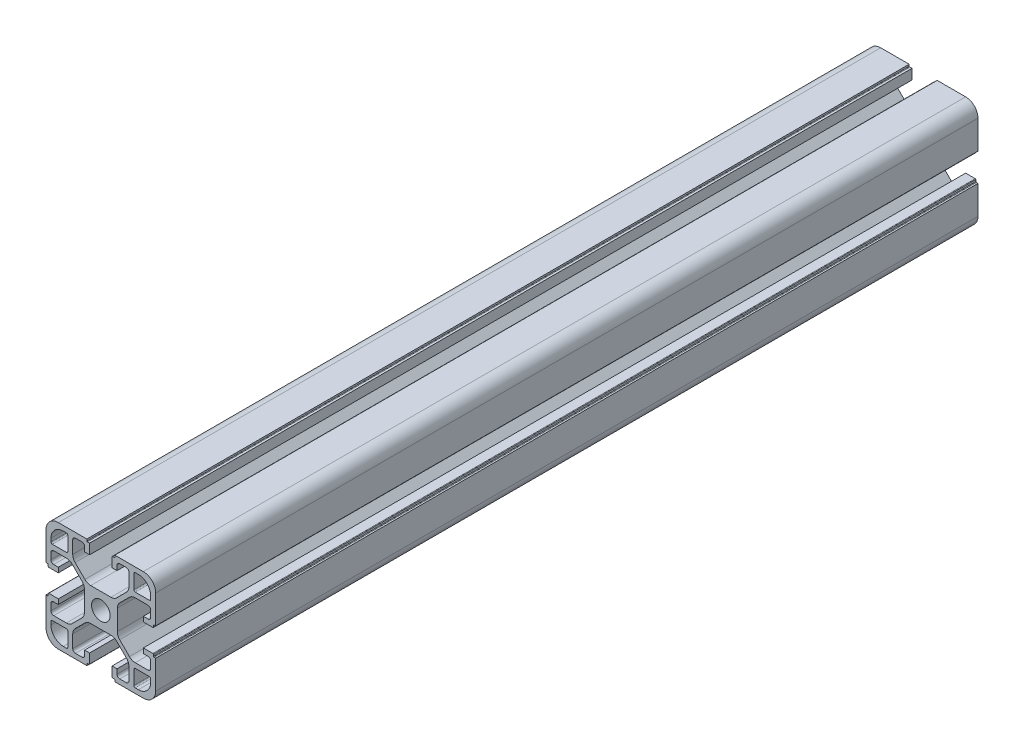
SolidWorks part; units mm, degrees
ref_plane "Front Plane" through (0, 0, 0) normal (0, 0, 1) x (1, 0, 0)
ref_plane "Top Plane" through (0, 0, 0) normal (0, 1, 0) x (1, 0, 0)
ref_plane "Right Plane" through (0, 0, 0) normal (1, 0, 0) x (0, 0, -1)
sketch "Sketch1" plane through (0, 0, 0) normal (0, 0, 1) x (1, 0, 0)
  line L0 (84.1702, 31.7204) -> (84.1702, 42.1204)
  line L1 (44.1702, 62.7204) -> (44.1702, 52.3204)
  line L2 (48.6702, 27.2204) -> (59.0702, 27.2204)
  line L3 (79.6702, 67.2204) -> (69.2702, 67.2204)
  line L4 (84.1702, 52.3204) -> (84.1702, 62.7204)
  line L5 (58.8702, 67.2204) -> (48.6702, 67.2204)
  line L6 (44.1702, 42.1204) -> (44.1702, 31.7204)
  line L7 (69.2702, 27.2204) -> (79.6702, 27.2204)
  line L8 (48.6702, 27.2204) -> (59.0702, 27.2204)
  line L9 (44.1702, 42.1204) -> (44.1702, 31.7204)
  line L10 (44.1702, 42.1204) -> (44.7702, 42.1204)
  line L11 (44.9702, 42.3204) -> (44.9702, 42.9204)
  line L12 (48.6702, 43.1204) -> (45.1702, 43.1204)
  line L13 (48.6702, 41.3204) -> (48.6702, 43.1204)
  line L14 (46.9702, 41.3204) -> (48.6702, 41.3204)
  line L15 (45.9702, 37.9704) -> (45.9702, 40.3204)
  line L16 (51.6169, 36.9704) -> (46.9702, 36.9704)
  line L17 (57.2915, 41.4024) -> (53.7382, 37.8491)
  line L18 (58.1702, 50.9171) -> (58.1702, 43.5237)
  line L19 (53.7382, 56.5917) -> (57.2915, 53.0384)
  line L20 (46.9702, 57.4704) -> (51.6169, 57.4704)
  line L21 (45.9702, 54.1204) -> (45.9702, 56.4704)
  line L22 (48.6702, 53.1204) -> (46.9702, 53.1204)
  line L23 (48.6702, 51.3204) -> (48.6702, 53.1204)
  line L24 (45.1702, 51.3204) -> (48.6702, 51.3204)
  line L25 (44.9702, 51.5204) -> (44.9702, 52.1204)
  line L26 (44.7702, 52.3204) -> (44.1702, 52.3204)
  line L27 (44.1702, 62.7204) -> (44.1702, 52.3204)
  line L28 (59.0702, 67.2204) -> (48.6702, 67.2204)
  line L29 (59.0702, 67.2204) -> (59.0702, 66.6204)
  line L30 (59.2702, 66.4204) -> (60.0702, 66.4204)
  line L31 (60.0702, 62.7204) -> (60.0702, 66.4204)
  line L32 (58.2702, 62.7204) -> (60.0702, 62.7204)
  line L33 (58.2702, 64.4204) -> (58.2702, 62.7204)
  line L34 (54.9202, 65.4204) -> (57.2702, 65.4204)
  line L35 (53.9202, 59.7737) -> (53.9202, 64.4204)
  line L36 (58.3522, 54.0991) -> (54.7989, 57.6524)
  line L37 (67.8669, 53.2204) -> (60.4735, 53.2204)
  line L38 (73.5415, 57.6524) -> (69.9882, 54.0991)
  line L39 (74.4202, 64.4204) -> (74.4202, 59.7737)
  line L40 (71.0702, 65.4204) -> (73.4202, 65.4204)
  line L41 (70.0702, 62.7204) -> (70.0702, 64.4204)
  line L42 (68.2702, 62.7204) -> (70.0702, 62.7204)
  line L43 (68.2702, 66.2204) -> (68.2702, 62.7204)
  line L44 (68.4702, 66.4204) -> (69.2702, 66.4204)
  line L45 (69.2702, 66.4204) -> (69.2702, 67.2204)
  line L46 (79.6702, 67.2204) -> (69.4702, 67.2204)
  line L47 (84.1702, 52.3204) -> (84.1702, 62.7204)
  line L48 (84.1702, 52.3204) -> (83.5702, 52.3204)
  line L49 (83.3702, 52.1204) -> (83.3702, 51.5204)
  line L50 (79.6702, 51.3204) -> (83.1702, 51.3204)
  line L51 (79.6702, 53.1204) -> (79.6702, 51.3204)
  line L52 (81.3702, 53.1204) -> (79.6702, 53.1204)
  line L53 (82.3702, 56.4704) -> (82.3702, 54.1204)
  line L54 (76.7235, 57.4704) -> (81.3702, 57.4704)
  line L55 (71.0489, 53.0384) -> (74.6022, 56.5917)
  line L56 (70.1702, 43.5237) -> (70.1702, 50.9171)
  line L57 (74.6022, 37.8491) -> (71.0489, 41.4024)
  line L58 (81.3702, 36.9704) -> (76.7235, 36.9704)
  line L59 (82.3702, 40.3204) -> (82.3702, 37.9704)
  line L60 (79.6702, 41.3204) -> (81.3702, 41.3204)
  line L61 (79.6702, 43.1204) -> (79.6702, 41.3204)
  line L62 (83.1702, 43.1204) -> (79.6702, 43.1204)
  line L63 (83.3702, 42.9204) -> (83.3702, 42.3204)
  line L64 (83.5702, 42.1204) -> (84.1702, 42.1204)
  line L65 (84.1702, 31.7204) -> (84.1702, 42.1204)
  line L66 (69.2702, 27.2204) -> (79.6702, 27.2204)
  line L67 (69.2702, 27.2204) -> (69.2702, 27.8204)
  line L68 (69.0702, 28.0204) -> (68.4702, 28.0204)
  line L69 (68.2702, 31.7204) -> (68.2702, 28.2204)
  line L70 (70.0702, 31.7204) -> (68.2702, 31.7204)
  line L71 (70.0702, 30.0204) -> (70.0702, 31.7204)
  line L72 (73.4202, 29.0204) -> (71.0702, 29.0204)
  line L73 (74.4202, 34.6671) -> (74.4202, 30.0204)
  line L74 (69.9882, 40.3417) -> (73.5415, 36.7884)
  line L75 (60.4735, 41.2204) -> (67.8669, 41.2204)
  line L76 (54.7989, 36.7884) -> (58.3522, 40.3417)
  line L77 (53.9202, 30.0204) -> (53.9202, 34.6671)
  line L78 (57.2702, 29.0204) -> (54.9202, 29.0204)
  line L79 (58.2702, 31.7204) -> (58.2702, 30.0204)
  line L80 (60.0702, 31.7204) -> (58.2702, 31.7204)
  line L81 (60.0702, 28.2204) -> (60.0702, 31.7204)
  line L82 (59.8702, 28.0204) -> (59.2702, 28.0204)
  line L83 (59.0702, 27.8204) -> (59.0702, 27.2204)
  line L84 (82.3702, 34.6704) -> (82.3702, 33.5204)
  line L85 (76.7202, 35.1704) -> (81.8702, 35.1704)
  line L86 (76.2202, 29.5204) -> (76.2202, 34.6704)
  line L87 (77.8702, 29.0204) -> (76.7202, 29.0204)
  line L88 (51.6202, 29.0204) -> (50.4702, 29.0204)
  line L89 (52.1202, 34.6704) -> (52.1202, 29.5204)
  line L90 (46.4702, 35.1704) -> (51.6202, 35.1704)
  line L91 (45.9702, 33.5204) -> (45.9702, 34.6704)
  line L92 (45.9702, 59.7704) -> (45.9702, 60.9204)
  line L93 (51.6202, 59.2704) -> (46.4702, 59.2704)
  line L94 (52.1202, 64.9204) -> (52.1202, 59.7704)
  line L95 (50.4702, 65.4204) -> (51.6202, 65.4204)
  line L96 (76.7202, 65.4204) -> (77.8702, 65.4204)
  line L97 (76.2202, 59.7704) -> (76.2202, 64.9204)
  line L98 (81.8702, 59.2704) -> (76.7202, 59.2704)
  line L99 (82.3702, 60.9204) -> (82.3702, 59.7704)
  line L100 (71.0702, 65.4204) -> (73.4202, 65.4204)
  line L101 (70.0702, 62.7204) -> (70.0702, 64.4204)
  line L102 (68.2702, 62.7204) -> (70.0702, 62.7204)
  line L103 (68.2702, 66.2204) -> (68.2702, 62.7204)
  line L104 (60.0702, 62.7204) -> (60.0702, 66.2204)
  line L105 (58.2702, 62.7204) -> (60.0702, 62.7204)
  line L106 (58.2702, 64.4204) -> (58.2702, 62.7204)
  line L107 (54.9202, 65.4204) -> (57.2702, 65.4204)
  line L108 (53.9202, 59.7737) -> (53.9202, 64.4204)
  line L109 (58.3522, 54.0991) -> (54.7989, 57.6524)
  line L110 (67.8669, 53.2204) -> (60.4735, 53.2204)
  line L111 (73.5415, 57.6524) -> (69.9882, 54.0991)
  line L112 (74.4202, 64.4204) -> (74.4202, 59.7737)
  line L113 (59.2702, 66.4204) -> (59.8702, 66.4204)
  line L114 (59.0702, 67.0204) -> (59.0702, 66.6204)
  line L115 (69.2702, 66.6204) -> (69.2702, 67.0204)
  line L116 (68.4702, 66.4204) -> (69.0702, 66.4204)
  line L117 (82.3702, 40.3204) -> (82.3702, 37.9704)
  line L118 (79.6702, 41.3204) -> (81.3702, 41.3204)
  line L119 (79.6702, 43.1204) -> (79.6702, 41.3204)
  line L120 (83.1702, 43.1204) -> (79.6702, 43.1204)
  line L121 (79.6702, 51.3204) -> (83.1702, 51.3204)
  line L122 (79.6702, 53.1204) -> (79.6702, 51.3204)
  line L123 (81.3702, 53.1204) -> (79.6702, 53.1204)
  line L124 (82.3702, 56.4704) -> (82.3702, 54.1204)
  line L125 (76.7235, 57.4704) -> (81.3702, 57.4704)
  line L126 (71.0489, 53.0384) -> (74.6022, 56.5917)
  line L127 (70.1702, 43.5237) -> (70.1702, 50.9171)
  line L128 (74.6022, 37.8491) -> (71.0489, 41.4024)
  line L129 (81.3702, 36.9704) -> (76.7235, 36.9704)
  line L130 (45.9702, 54.1204) -> (45.9702, 56.4704)
  line L131 (48.6702, 53.1204) -> (46.9702, 53.1204)
  line L132 (48.6702, 51.3204) -> (48.6702, 53.1204)
  line L133 (45.1702, 51.3204) -> (48.6702, 51.3204)
  line L134 (48.6702, 43.1204) -> (45.1702, 43.1204)
  line L135 (48.6702, 41.3204) -> (48.6702, 43.1204)
  line L136 (46.9702, 41.3204) -> (48.6702, 41.3204)
  line L137 (45.9702, 37.9704) -> (45.9702, 40.3204)
  line L138 (51.6169, 36.9704) -> (46.9702, 36.9704)
  line L139 (57.2915, 41.4024) -> (53.7382, 37.8491)
  line L140 (58.1702, 50.9171) -> (58.1702, 43.5237)
  line L141 (53.7382, 56.5917) -> (57.2915, 53.0384)
  line L142 (46.9702, 57.4704) -> (51.6169, 57.4704)
  line L143 (57.2702, 29.0204) -> (54.9202, 29.0204)
  line L144 (58.2702, 31.7204) -> (58.2702, 30.0204)
  line L145 (60.0702, 31.7204) -> (58.2702, 31.7204)
  line L146 (60.0702, 28.2204) -> (60.0702, 31.7204)
  line L147 (68.2702, 31.7204) -> (68.2702, 28.2204)
  line L148 (70.0702, 31.7204) -> (68.2702, 31.7204)
  line L149 (70.0702, 30.0204) -> (70.0702, 31.7204)
  line L150 (73.4202, 29.0204) -> (71.0702, 29.0204)
  line L151 (74.4202, 34.6671) -> (74.4202, 30.0204)
  line L152 (69.9882, 40.3417) -> (73.5415, 36.7884)
  line L153 (60.4735, 41.2204) -> (67.8669, 41.2204)
  line L154 (54.7989, 36.7884) -> (58.3522, 40.3417)
  line L155 (53.9202, 30.0204) -> (53.9202, 34.6671)
  line L156 (69.0702, 28.0204) -> (68.4702, 28.0204)
  line L157 (69.2702, 27.2204) -> (69.2702, 27.8204)
  line L158 (59.0702, 27.8204) -> (59.0702, 27.2204)
  line L159 (59.8702, 28.0204) -> (59.2702, 28.0204)
  line L160 (44.9702, 42.3204) -> (44.9702, 42.9204)
  line L161 (44.1702, 42.1204) -> (44.7702, 42.1204)
  line L162 (44.7702, 52.3204) -> (44.1702, 52.3204)
  line L163 (44.9702, 51.5204) -> (44.9702, 52.1204)
  line L164 (83.3702, 52.1204) -> (83.3702, 51.5204)
  line L165 (84.1702, 52.3204) -> (83.5702, 52.3204)
  line L166 (83.5702, 42.1204) -> (84.1702, 42.1204)
  line L167 (83.3702, 42.9204) -> (83.3702, 42.3204)
  line L168 (76.2202, 59.7704) -> (76.2202, 64.9204)
  line L169 (81.8702, 59.2704) -> (76.7202, 59.2704)
  line L170 (82.3702, 60.9204) -> (82.3702, 59.7704)
  line L171 (76.7202, 65.4204) -> (77.8702, 65.4204)
  line L172 (51.6202, 59.2704) -> (46.4702, 59.2704)
  line L173 (52.1202, 64.9204) -> (52.1202, 59.7704)
  line L174 (50.4702, 65.4204) -> (51.6202, 65.4204)
  line L175 (45.9702, 59.7704) -> (45.9702, 60.9204)
  line L176 (52.1202, 34.6704) -> (52.1202, 29.5204)
  line L177 (46.4702, 35.1704) -> (51.6202, 35.1704)
  line L178 (45.9702, 33.5204) -> (45.9702, 34.6704)
  line L179 (51.6202, 29.0204) -> (50.4702, 29.0204)
  line L180 (76.7202, 35.1704) -> (81.8702, 35.1704)
  line L181 (76.2202, 29.5204) -> (76.2202, 34.6704)
  line L182 (77.8702, 29.0204) -> (76.7202, 29.0204)
  line L183 (82.3702, 34.6704) -> (82.3702, 33.5204)
  arc A0 (60.7702, 47.2204) -> (67.5702, 47.2204) centre (64.1702, 47.2204) ccw
  arc A1 (44.1702, 31.7204) -> (48.6702, 27.2204) centre (48.6702, 31.7204) ccw
  arc A2 (44.7702, 42.1204) -> (44.9702, 42.3204) centre (44.7702, 42.3204) ccw
  arc A3 (45.1702, 43.1204) -> (44.9702, 42.9204) centre (45.1702, 42.9204) ccw
  arc A4 (46.9702, 41.3204) -> (45.9702, 40.3204) centre (46.9702, 40.3204) ccw
  arc A5 (45.9702, 37.9704) -> (46.9702, 36.9704) centre (46.9702, 37.9704) ccw
  arc A6 (51.6169, 36.9704) -> (53.7382, 37.8491) centre (51.6169, 39.9704) ccw
  arc A7 (57.2915, 41.4024) -> (58.1702, 43.5237) centre (55.1702, 43.5237) ccw
  arc A8 (58.1702, 50.9171) -> (57.2915, 53.0384) centre (55.1702, 50.9171) ccw
  arc A9 (53.7382, 56.5917) -> (51.6169, 57.4704) centre (51.6169, 54.4704) ccw
  arc A10 (46.9702, 57.4704) -> (45.9702, 56.4704) centre (46.9702, 56.4704) ccw
  arc A11 (45.9702, 54.1204) -> (46.9702, 53.1204) centre (46.9702, 54.1204) ccw
  arc A12 (44.9702, 51.5204) -> (45.1702, 51.3204) centre (45.1702, 51.5204) ccw
  arc A13 (44.9702, 52.1204) -> (44.7702, 52.3204) centre (44.7702, 52.1204) ccw
  arc A14 (48.6702, 67.2204) -> (44.1702, 62.7204) centre (48.6702, 62.7204) ccw
  arc A15 (59.0702, 66.6204) -> (59.2702, 66.4204) centre (59.2702, 66.6204) ccw
  arc A16 (58.2702, 64.4204) -> (57.2702, 65.4204) centre (57.2702, 64.4204) ccw
  arc A17 (54.9202, 65.4204) -> (53.9202, 64.4204) centre (54.9202, 64.4204) ccw
  arc A18 (53.9202, 59.7737) -> (54.7989, 57.6524) centre (56.9202, 59.7737) ccw
  arc A19 (58.3522, 54.0991) -> (60.4735, 53.2204) centre (60.4735, 56.2204) ccw
  arc A20 (67.8669, 53.2204) -> (69.9882, 54.0991) centre (67.8669, 56.2204) ccw
  arc A21 (73.5415, 57.6524) -> (74.4202, 59.7737) centre (71.4202, 59.7737) ccw
  arc A22 (74.4202, 64.4204) -> (73.4202, 65.4204) centre (73.4202, 64.4204) ccw
  arc A23 (71.0702, 65.4204) -> (70.0702, 64.4204) centre (71.0702, 64.4204) ccw
  arc A24 (68.4702, 66.4204) -> (68.2702, 66.2204) centre (68.4702, 66.2204) ccw
  arc A25 (84.1702, 62.7204) -> (79.6702, 67.2204) centre (79.6702, 62.7204) ccw
  arc A26 (83.5702, 52.3204) -> (83.3702, 52.1204) centre (83.5702, 52.1204) ccw
  arc A27 (83.1702, 51.3204) -> (83.3702, 51.5204) centre (83.1702, 51.5204) ccw
  arc A28 (81.3702, 53.1204) -> (82.3702, 54.1204) centre (81.3702, 54.1204) ccw
  arc A29 (82.3702, 56.4704) -> (81.3702, 57.4704) centre (81.3702, 56.4704) ccw
  arc A30 (76.7235, 57.4704) -> (74.6022, 56.5917) centre (76.7235, 54.4704) ccw
  arc A31 (71.0489, 53.0384) -> (70.1702, 50.9171) centre (73.1702, 50.9171) ccw
  arc A32 (70.1702, 43.5237) -> (71.0489, 41.4024) centre (73.1702, 43.5237) ccw
  arc A33 (74.6022, 37.8491) -> (76.7235, 36.9704) centre (76.7235, 39.9704) ccw
  arc A34 (81.3702, 36.9704) -> (82.3702, 37.9704) centre (81.3702, 37.9704) ccw
  arc A35 (82.3702, 40.3204) -> (81.3702, 41.3204) centre (81.3702, 40.3204) ccw
  arc A36 (83.3702, 42.9204) -> (83.1702, 43.1204) centre (83.1702, 42.9204) ccw
  arc A37 (83.3702, 42.3204) -> (83.5702, 42.1204) centre (83.5702, 42.3204) ccw
  arc A38 (79.6702, 27.2204) -> (84.1702, 31.7204) centre (79.6702, 31.7204) ccw
  arc A39 (69.2702, 27.8204) -> (69.0702, 28.0204) centre (69.0702, 27.8204) ccw
  arc A40 (68.2702, 28.2204) -> (68.4702, 28.0204) centre (68.4702, 28.2204) ccw
  arc A41 (70.0702, 30.0204) -> (71.0702, 29.0204) centre (71.0702, 30.0204) ccw
  arc A42 (73.4202, 29.0204) -> (74.4202, 30.0204) centre (73.4202, 30.0204) ccw
  arc A43 (74.4202, 34.6671) -> (73.5415, 36.7884) centre (71.4202, 34.6671) ccw
  arc A44 (69.9882, 40.3417) -> (67.8669, 41.2204) centre (67.8669, 38.2204) ccw
  arc A45 (60.4735, 41.2204) -> (58.3522, 40.3417) centre (60.4735, 38.2204) ccw
  arc A46 (54.7989, 36.7884) -> (53.9202, 34.6671) centre (56.9202, 34.6671) ccw
  arc A47 (53.9202, 30.0204) -> (54.9202, 29.0204) centre (54.9202, 30.0204) ccw
  arc A48 (57.2702, 29.0204) -> (58.2702, 30.0204) centre (57.2702, 30.0204) ccw
  arc A49 (59.8702, 28.0204) -> (60.0702, 28.2204) centre (59.8702, 28.2204) ccw
  arc A50 (59.2702, 28.0204) -> (59.0702, 27.8204) centre (59.2702, 27.8204) ccw
  arc A51 (82.3702, 34.6704) -> (81.8702, 35.1704) centre (81.8702, 34.6704) ccw
  arc A52 (76.7202, 35.1704) -> (76.2202, 34.6704) centre (76.7202, 34.6704) ccw
  arc A53 (76.2202, 29.5204) -> (76.7202, 29.0204) centre (76.7202, 29.5204) ccw
  arc A54 (77.8702, 29.0204) -> (82.3702, 33.5204) centre (77.8702, 33.5204) ccw
  arc A55 (51.6202, 29.0204) -> (52.1202, 29.5204) centre (51.6202, 29.5204) ccw
  arc A56 (52.1202, 34.6704) -> (51.6202, 35.1704) centre (51.6202, 34.6704) ccw
  arc A57 (46.4702, 35.1704) -> (45.9702, 34.6704) centre (46.4702, 34.6704) ccw
  arc A58 (45.9702, 33.5204) -> (50.4702, 29.0204) centre (50.4702, 33.5204) ccw
  arc A59 (45.9702, 59.7704) -> (46.4702, 59.2704) centre (46.4702, 59.7704) ccw
  arc A60 (51.6202, 59.2704) -> (52.1202, 59.7704) centre (51.6202, 59.7704) ccw
  arc A61 (52.1202, 64.9204) -> (51.6202, 65.4204) centre (51.6202, 64.9204) ccw
  arc A62 (50.4702, 65.4204) -> (45.9702, 60.9204) centre (50.4702, 60.9204) ccw
  arc A63 (76.7202, 65.4204) -> (76.2202, 64.9204) centre (76.7202, 64.9204) ccw
  arc A64 (76.2202, 59.7704) -> (76.7202, 59.2704) centre (76.7202, 59.7704) ccw
  arc A65 (81.8702, 59.2704) -> (82.3702, 59.7704) centre (81.8702, 59.7704) ccw
  arc A66 (82.3702, 60.9204) -> (77.8702, 65.4204) centre (77.8702, 60.9204) ccw
  arc A67 (67.5702, 47.2204) -> (60.7702, 47.2204) centre (64.1702, 47.2204) ccw
  arc A68 (60.7702, 47.2204) -> (67.5702, 47.2204) centre (64.1702, 47.2204) ccw
  arc A69 (67.5702, 47.2204) -> (60.7702, 47.2204) centre (64.1702, 47.2204) ccw
  arc A70 (71.0702, 65.4204) -> (70.0702, 64.4204) centre (71.0702, 64.4204) ccw
  arc A71 (54.9202, 65.4204) -> (53.9202, 64.4204) centre (54.9202, 64.4204) ccw
  arc A72 (58.2702, 64.4204) -> (57.2702, 65.4204) centre (57.2702, 64.4204) ccw
  arc A73 (74.4202, 64.4204) -> (73.4202, 65.4204) centre (73.4202, 64.4204) ccw
  arc A74 (68.4702, 66.4204) -> (68.2702, 66.2204) centre (68.4702, 66.2204) ccw
  arc A75 (59.0702, 66.6204) -> (59.2702, 66.4204) centre (59.2702, 66.6204) ccw
  arc A76 (82.3702, 40.3204) -> (81.3702, 41.3204) centre (81.3702, 40.3204) ccw
  arc A77 (82.3702, 56.4704) -> (81.3702, 57.4704) centre (81.3702, 56.4704) ccw
  arc A78 (81.3702, 53.1204) -> (82.3702, 54.1204) centre (81.3702, 54.1204) ccw
  arc A79 (81.3702, 36.9704) -> (82.3702, 37.9704) centre (81.3702, 37.9704) ccw
  arc A80 (57.2702, 29.0204) -> (58.2702, 30.0204) centre (57.2702, 30.0204) ccw
  arc A81 (73.4202, 29.0204) -> (74.4202, 30.0204) centre (73.4202, 30.0204) ccw
  arc A82 (70.0702, 30.0204) -> (71.0702, 29.0204) centre (71.0702, 30.0204) ccw
  arc A83 (53.9202, 30.0204) -> (54.9202, 29.0204) centre (54.9202, 30.0204) ccw
  arc A84 (45.9702, 54.1204) -> (46.9702, 53.1204) centre (46.9702, 54.1204) ccw
  arc A85 (45.9702, 37.9704) -> (46.9702, 36.9704) centre (46.9702, 37.9704) ccw
  arc A86 (46.9702, 41.3204) -> (45.9702, 40.3204) centre (46.9702, 40.3204) ccw
  arc A87 (46.9702, 57.4704) -> (45.9702, 56.4704) centre (46.9702, 56.4704) ccw
  arc A88 (83.1702, 51.3204) -> (83.3702, 51.5204) centre (83.1702, 51.5204) ccw
  arc A89 (83.3702, 42.9204) -> (83.1702, 43.1204) centre (83.1702, 42.9204) ccw
  arc A90 (83.3702, 42.3204) -> (83.5702, 42.1204) centre (83.5702, 42.3204) ccw
  arc A91 (83.5702, 52.3204) -> (83.3702, 52.1204) centre (83.5702, 52.1204) ccw
  arc A92 (68.2702, 28.2204) -> (68.4702, 28.0204) centre (68.4702, 28.2204) ccw
  arc A93 (59.8702, 28.0204) -> (60.0702, 28.2204) centre (59.8702, 28.2204) ccw
  arc A94 (59.2702, 28.0204) -> (59.0702, 27.8204) centre (59.2702, 27.8204) ccw
  arc A95 (69.2702, 27.8204) -> (69.0702, 28.0204) centre (69.0702, 27.8204) ccw
  arc A96 (45.1702, 43.1204) -> (44.9702, 42.9204) centre (45.1702, 42.9204) ccw
  arc A97 (44.9702, 51.5204) -> (45.1702, 51.3204) centre (45.1702, 51.5204) ccw
  arc A98 (44.9702, 52.1204) -> (44.7702, 52.3204) centre (44.7702, 52.1204) ccw
  arc A99 (44.7702, 42.1204) -> (44.9702, 42.3204) centre (44.7702, 42.3204) ccw
  arc A100 (44.1702, 31.7204) -> (48.6702, 27.2204) centre (48.6702, 31.7204) ccw
  arc A101 (79.6702, 27.2204) -> (84.1702, 31.7204) centre (79.6702, 31.7204) ccw
  arc A102 (48.6702, 67.2204) -> (44.1702, 62.7204) centre (48.6702, 62.7204) ccw
  arc A103 (84.1702, 62.7204) -> (79.6702, 67.2204) centre (79.6702, 62.7204) ccw
  arc A104 (82.3702, 60.9204) -> (77.8702, 65.4204) centre (77.8702, 60.9204) ccw
  arc A105 (81.8702, 59.2704) -> (82.3702, 59.7704) centre (81.8702, 59.7704) ccw
  arc A106 (76.7202, 65.4204) -> (76.2202, 64.9204) centre (76.7202, 64.9204) ccw
  arc A107 (76.2202, 59.7704) -> (76.7202, 59.2704) centre (76.7202, 59.7704) ccw
  arc A108 (50.4702, 65.4204) -> (45.9702, 60.9204) centre (50.4702, 60.9204) ccw
  arc A109 (45.9702, 33.5204) -> (50.4702, 29.0204) centre (50.4702, 33.5204) ccw
  arc A110 (77.8702, 29.0204) -> (82.3702, 33.5204) centre (77.8702, 33.5204) ccw
  arc A111 (76.2202, 29.5204) -> (76.7202, 29.0204) centre (76.7202, 29.5204) ccw
  arc A112 (82.3702, 34.6704) -> (81.8702, 35.1704) centre (81.8702, 34.6704) ccw
  arc A113 (76.7202, 35.1704) -> (76.2202, 34.6704) centre (76.7202, 34.6704) ccw
  arc A114 (46.4702, 35.1704) -> (45.9702, 34.6704) centre (46.4702, 34.6704) ccw
  arc A115 (51.6202, 29.0204) -> (52.1202, 29.5204) centre (51.6202, 29.5204) ccw
  arc A116 (52.1202, 34.6704) -> (51.6202, 35.1704) centre (51.6202, 34.6704) ccw
  arc A117 (52.1202, 64.9204) -> (51.6202, 65.4204) centre (51.6202, 64.9204) ccw
  arc A118 (45.9702, 59.7704) -> (46.4702, 59.2704) centre (46.4702, 59.7704) ccw
  arc A119 (51.6202, 59.2704) -> (52.1202, 59.7704) centre (51.6202, 59.7704) ccw
  arc A120 (74.6022, 37.8491) -> (76.7235, 36.9704) centre (76.7235, 39.9704) ccw
  arc A121 (70.1702, 43.5237) -> (71.0489, 41.4024) centre (73.1702, 43.5237) ccw
  arc A122 (74.4202, 34.6671) -> (73.5415, 36.7884) centre (71.4202, 34.6671) ccw
  arc A123 (69.9882, 40.3417) -> (67.8669, 41.2204) centre (67.8669, 38.2204) ccw
  arc A124 (54.7989, 36.7884) -> (53.9202, 34.6671) centre (56.9202, 34.6671) ccw
  arc A125 (60.4735, 41.2204) -> (58.3522, 40.3417) centre (60.4735, 38.2204) ccw
  arc A126 (51.6169, 36.9704) -> (53.7382, 37.8491) centre (51.6169, 39.9704) ccw
  arc A127 (57.2915, 41.4024) -> (58.1702, 43.5237) centre (55.1702, 43.5237) ccw
  arc A128 (58.1702, 50.9171) -> (57.2915, 53.0384) centre (55.1702, 50.9171) ccw
  arc A129 (53.7382, 56.5917) -> (51.6169, 57.4704) centre (51.6169, 54.4704) ccw
  arc A130 (53.9202, 59.7737) -> (54.7989, 57.6524) centre (56.9202, 59.7737) ccw
  arc A131 (58.3522, 54.0991) -> (60.4735, 53.2204) centre (60.4735, 56.2204) ccw
  arc A132 (67.8669, 53.2204) -> (69.9882, 54.0991) centre (67.8669, 56.2204) ccw
  arc A133 (71.0489, 53.0384) -> (70.1702, 50.9171) centre (73.1702, 50.9171) ccw
  arc A134 (76.7235, 57.4704) -> (74.6022, 56.5917) centre (76.7235, 54.4704) ccw
  arc A135 (73.5415, 57.6524) -> (74.4202, 59.7737) centre (71.4202, 59.7737) ccw
extrude "Boss-Extrude1" add sketch "Sketch1" along normal blind 300 contours A50 L82 A49 L81 L80 L79 A48 L78 A47 L77 A46 L76 A45 L75 A44 L74 A43 L73 A42 L72 A41 L71 L70 L69 A40 L68 A39 L67 L7 A38 L0 L64 A37 L63 A36 L62 L61 L60 A35 L59 A34 L58 A33 L57 A32 L56 A31 L55 A30 L54 A29
